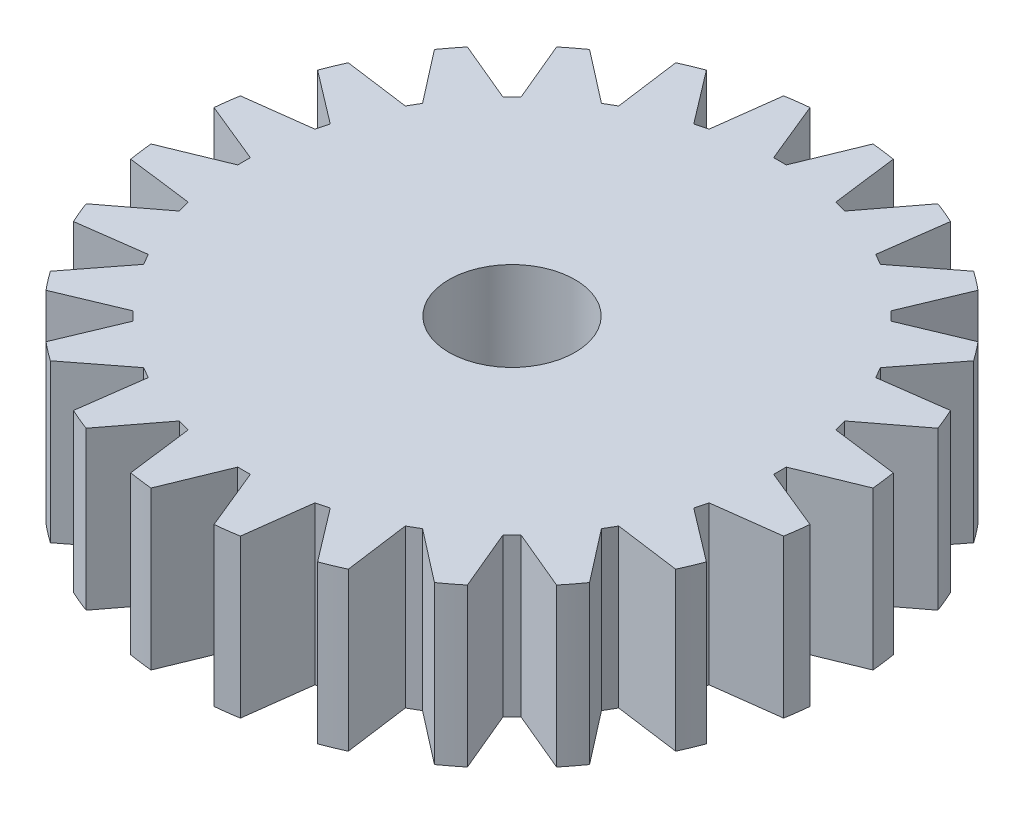
SolidWorks part; units mm, degrees
ref_plane "Front Plane" through (0, 0, 0) normal (0, 0, 1) x (1, 0, 0)
ref_plane "Top Plane" through (0, 0, 0) normal (0, 1, 0) x (1, 0, 0)
ref_plane "Right Plane" through (0, 0, 0) normal (1, 0, 0) x (0, 0, -1)
sketch "Sketch1" plane through (0, 0, 0) normal (0, 1, 0) x (1, 0, 0)
  circle A0 centre (0, 0) radius 10.5
  dimension "D1" = 21
extrude "Boss-Extrude1" add sketch "Sketch1" along normal blind 5
sketch "Sketch2" plane through (0, 5, 0) normal (0, 1, 0) x (1, 0, 0)
  circle A0 centre (0, 0) radius 2
  dimension "D1" = 4
extrude "Cut-Extrude1" cut sketch "Sketch2" against normal through all
sketch "Sketch3" plane through (0, 5, 0) normal (0, 1, 0) x (1, 0, 0)
  line L0 (0, 8.5) -> (0.2, 8.5)
  line L1 (0.2, 8.5) -> (1, 10.4523)
  line L2 (1, 10.4523) -> (1, 11.8214)
  line L3 (1, 11.8214) -> (-1, 11.8214)
  line L4 (-1, 11.8214) -> (-1, 10.4523)
  line L5 (-1, 10.4523) -> (-0.2, 8.5)
  line L6 (-0.2, 8.5) -> (0, 8.5)
  line L7 (0, 8.5) -> (0, 0) construction
  circle A0 centre (0, 0) radius 10.5 construction
  dimension "D1" = 0.2
  dimension "D2" = 0.2
  dimension "D3" = 0.8
  dimension "D4" = 0.8
  dimension "D5" = 8.5
extrude "Cut-Extrude2" cut sketch "Sketch3" against normal blind 5
pattern_circular "CirPattern1" count 24 over 360 about axis through (0, 0, 0) along (0, 1, 0) of "Cut-Extrude2"
